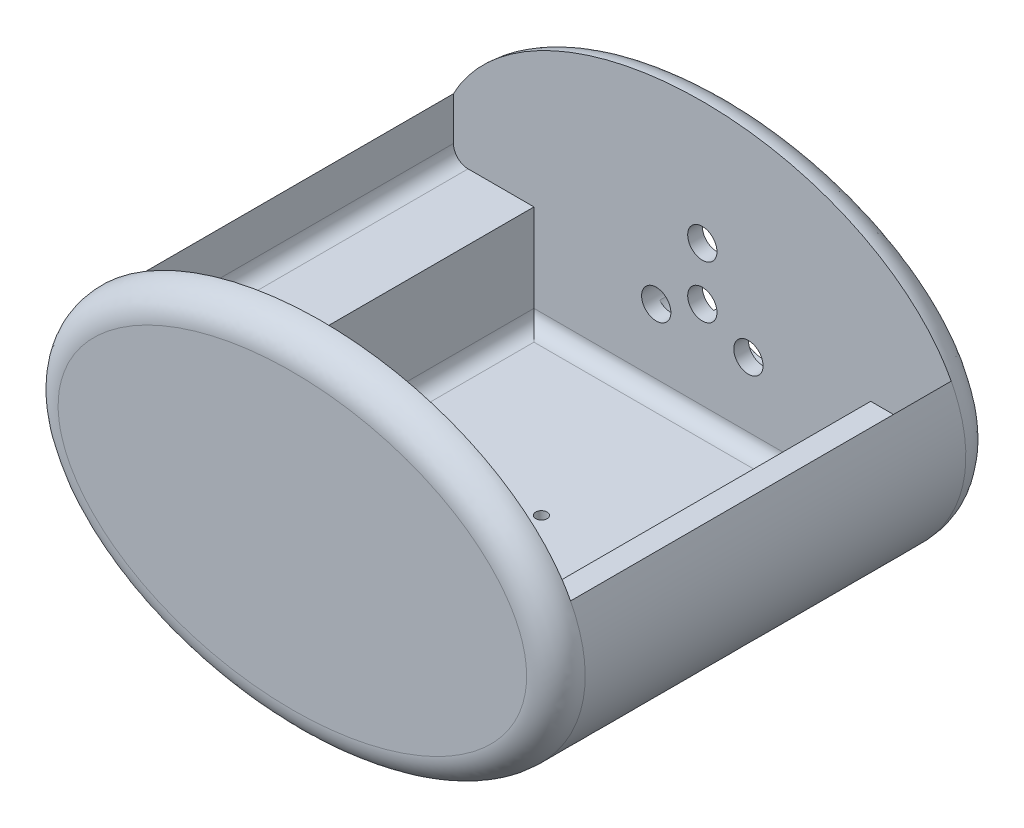
SolidWorks part; units mm, degrees
ref_plane "Front Plane" through (0, 0, 0) normal (0, 0, 1) x (1, 0, 0)
ref_plane "Top Plane" through (0, 0, 0) normal (0, 1, 0) x (1, 0, 0)
ref_plane "Right Plane" through (0, 0, 0) normal (1, 0, 0) x (0, 0, -1)
sketch "Sketch1" plane through (0, 0, 0) normal (0, 0, 1) x (1, 0, 0)
  ellipse E0 centre (0, 0) end of major axis (-22.86, 0) minor radius 15.24
extrude "Boss-Extrude4" add sketch "Sketch1" along normal blind 45.72 contours E0
sketch "Sketch4" plane through (0, 0, 45.72) normal (0, 0, 1) x (1, 0, 0)
  line L1 (14.605, -8.89) -> (-14.605, -8.89)
  line L2 (14.605, -8.89) -> (14.605, 8.89)
  line L3 (14.605, 8.89) -> (-14.605, 8.89)
  line L4 (-14.605, -8.89) -> (-14.605, 8.89)
  dimension "D1" = 8.89
  dimension "D2" = 17.78
  dimension "D3" = 14.605
  dimension "D4" = 29.21
extrude "Cut-Extrude2" cut sketch "Sketch4" against normal blind 33.02 from offset 10.16 offset against normal yes
sketch "Sketch7" plane through (0, 0, 0) normal (1, 0, 0) x (0, 0, -1)
  line L0 (-45.72, 15.24) -> (-45.72, -15.24) construction
  line L1 (-38.1, 16.1024) -> (-52.7439, 16.1024)
  line L2 (-38.1, 16.1024) -> (-38.1, -19.4576)
  line L3 (-38.1, -19.4576) -> (-52.7439, -19.4576)
  line L4 (-52.7439, 16.1024) -> (-52.7439, -19.4576)
  dimension "D1" = 7.62
  dimension "D2" = 14.6439
  dimension "D3" = 35.56
extrude "Cut-Extrude4" cut sketch "Sketch7" against normal blind 33.02 and the other way blind 33.02
sketch "Sketch8" plane through (0, 0, 0) normal (0, 0, 1) x (1, 0, 0)
  circle A0 centre (0, 0) radius 1.27
  circle A1 centre (3.9984, -1.9992) radius 1.27
  circle A2 centre (-3.9984, -1.9992) radius 1.27
  circle A3 centre (0, 4.572) radius 1.27
  dimension "D1" = 4.4704
  dimension "D2" = 2.54
  dimension "D3" = 2.54
  dimension "D4" = 2.54
  dimension "D5" = 2.54
  dimension "D7" = 4.572
  dimension "D8" = 4.4704
extrude "Cut-Extrude5" cut sketch "Sketch8" along normal blind 2.54
fillet "Fillet1" radius 2.54 1 edges at (-22.86, 0, 0)
fillet "Fillet2" radius 2.54 1 edges at (-22.86, 0, 38.1)
sketch "Sketch12" plane through (0, 0, 0) normal (0, 0, -1) x (-1, 0, 0)
  line L1 (-21.59, 0) -> (21.59, 0)
  line L2 (-21.59, 0) -> (-21.59, 19.05)
  line L3 (-21.59, 19.05) -> (21.59, 19.05)
  line L4 (21.59, 0) -> (21.59, 19.05)
  dimension "D1" = 43.18
  dimension "D2" = 19.05
  dimension "D3" = 19.05
  dimension "D4" = 21.59
extrude "Cut-Extrude11" cut sketch "Sketch12" against normal blind 33.02 from offset 2.54 offset against normal yes
fillet "Fillet3" radius 1.27 4 edges at (-14.605, -8.89, 19.05) (0, -8.89, 2.54) (14.605, -8.89, 19.05) (0, -8.89, 35.56)
sketch "Sketch13" plane through (0, -8.89, 0) normal (0, 1, 0) x (1, 0, 0)
  line L0 (14.605, -35.56) -> (-14.605, -35.56) construction
  line L1 (-2.54, -20.828) -> (2.54, -20.828)
  line L2 (-2.54, -20.828) -> (-2.54, -15.748)
  line L3 (-2.54, -15.748) -> (2.54, -15.748)
  line L4 (2.54, -20.828) -> (2.54, -15.748)
  dimension "D1" = 5.08
  dimension "D2" = 5.08
  dimension "D3" = 2.54
  dimension "D4" = 14.732
extrude "Cut-Extrude13" cut sketch "Sketch13" against normal through all from offset 2.54 offset against normal yes
sketch "Sketch14" plane through (0, -11.43, 0) normal (0, -1, 0) x (1, 0, 0)
  line L0 (-2.54, 20.828) -> (2.54, 20.828) construction
  line L1 (2.54, 20.828) -> (2.54, 15.748) construction
  line L2 (2.54, 15.748) -> (-2.54, 15.748) construction
  circle A0 centre (0, 20.078) radius 0.5
  circle A1 centre (0, 16.498) radius 0.5
  dimension "D1" = 1
  dimension "D4" = 1
  dimension "D2" = 0.75
  dimension "D3" = 2.54
  dimension "D5" = 0.75
  dimension "D6" = 2.54
extrude "Cut-Extrude14" cut sketch "Sketch14" against normal through all both and the other way through all
sketch "Sketch16" plane through (0, 0, 0) normal (0, 0, -1) x (-1, 0, 0)
  circle A0 centre (2.7942, -1.506) radius 2.54
  circle A1 centre (0.0002, 3.3334) radius 2.54
  circle A2 centre (-2.7938, -1.506) radius 2.54
  dimension "D1" = 5.08
  dimension "D2" = 5.08
  dimension "D3" = 5.08
  dimension "D7" = 2.7938
  dimension "D4" = 5.588
  dimension "D5" = 5.588
  dimension "D6" = 5.588
  dimension "D8" = 2.7942
  dimension "D9" = 3.3334
extrude "Cut-Extrude15" cut sketch "Sketch16" against normal blind 1.27
fillet "Fillet4" radius 1.27 2 edges at (-21.59, 0, 19.05) (21.59, 0, 19.05)
